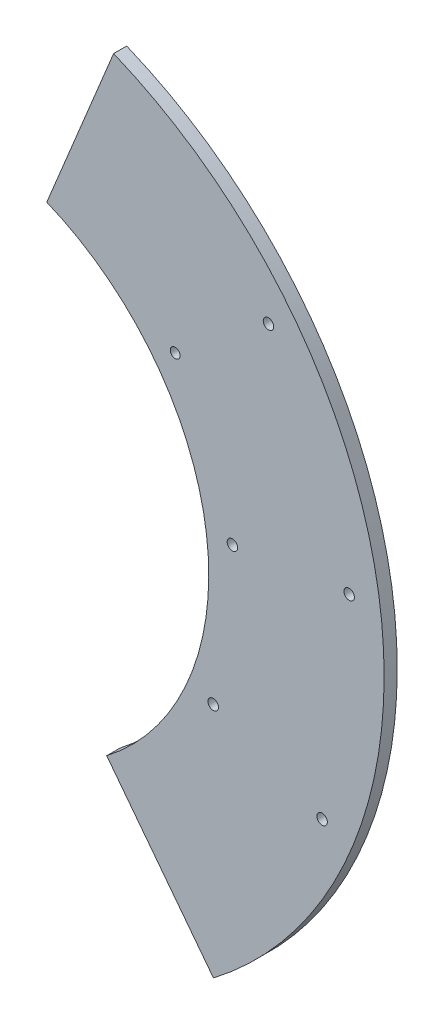
SolidWorks part; units mm, degrees
ref_plane "Plan de face" through (0, 0, 0) normal (0, 0, 1) x (1, 0, 0)
ref_plane "Plan de dessus" through (0, 0, 0) normal (0, 1, 0) x (1, 0, 0)
ref_plane "Plan de droite" through (0, 0, 0) normal (1, 0, 0) x (0, 0, -1)
sketch "Esquisse1" plane through (0, 0, 0) normal (0, 0, 1) x (1, 0, 0)
  line L2 (-2, 166.988) -> (-2, 99.98)
  line L3 (-2, -99.98) -> (-2, -166.988)
  arc A1 (0, -133.5) -> (0, 133.5) centre (0, 0) ccw
  arc A12 (-2, -166.988) -> (-2, 166.988) centre (0, 0) ccw
  arc A13 (-2, -99.98) -> (-2, 99.98) centre (0, 0) ccw
  point P0 (0, 0)
  point P1 (133.5, 0)
  point P4 (102, 0)
  point P5 (0, 0)
  point P7 (0, 165)
  point P8 (0, 102)
  point P9 (0, -102)
  point P10 (0, -165)
  point P11 (157.7903, 48.2413)
  point P42 (0, 0)
extrude "Boss.-Extru.2" add sketch "Esquisse1" along normal blind 5
sketch "Esquisse2" plane through (0, 0, 5) normal (0, 0, 1) x (1, 0, 0)
  line L0 (38.1129, 92.4522) -> (63.6486, 154.3951)
  line L1 (41.1619, 99.8484) -> (38.1129, 92.4522) construction
  line L2 (63.6486, 154.3951) -> (59.8373, 145.1499) construction
  line L3 (63.6486, 154.3951) -> (68.0288, 172.2752)
  line L4 (68.0288, 172.2752) -> (-24.9555, 192.9143)
  line L5 (-24.9555, 192.9143) -> (-14.9881, 82.8015)
  line L6 (-14.9881, 82.8015) -> (56.1922, 19.6454)
  line L7 (56.1922, 19.6454) -> (53.907, -84.2261)
  line L8 (53.907, -84.2261) -> (102.4159, -133.0072)
  line L9 (217.8754, -118.1368) -> (49.268, -139.8523) construction
  line L10 (95.7849, -124.3956) -> (101.8858, -132.3188) construction
  line L11 (102.4159, -133.0072) -> (102.4159, -156.0251)
  line L12 (102.4159, -156.0251) -> (-11.1483, -184.4376)
  line L13 (-11.1483, -184.4376) -> (38.1129, 92.4522)
  arc A0 (-2, -99.98) -> (-2, 99.98) centre (0, 0) ccw construction
  arc A1 (-2, -166.988) -> (-2, 166.988) centre (0, 0) ccw construction
  arc M1 (-2, 99.98) -> (-2, -99.98) centre (0, 0) cw
  line M2 (-2, -99.98) -> (-2, -166.988)
  arc M3 (-2, -166.988) -> (-2, 166.988) centre (0, 0) ccw
  line M4 (-2, 166.988) -> (-2, 99.98)
extrude "Enlèv. mat.-Extru.1" cut sketch "Esquisse2" against normal blind 10 contours L13 L11 L8 M2 M3 M1 | L0 M1 M3 M4
sketch "Esquisse3" plane through (0, 0, 5) normal (0, 0, 1) x (1, 0, 0)
  line L1 (25.4042, -95.1848) -> (-45.4208, -95.1848)
  line L2 (25.4042, -95.1848) -> (25.4042, -147.3571)
  line L3 (25.4042, -147.3571) -> (-45.4208, -147.3571)
  line L4 (-45.4208, -95.1848) -> (-45.4208, -147.3571)
extrude "Enlèv. mat.-Extru.2" cut sketch "Esquisse3" against normal blind 10
sketch "Esquisse4" plane through (0, 0, 5) normal (0, 0, 1) x (1, 0, 0)
  circle A0 centre (109.0346, 14.5413) radius 2
  circle A1 centre (101.6974, -41.9242) radius 2
  circle A2 centre (87.1561, 67.1104) radius 1.8701
  circle A3 centre (122.8109, 94.5647) radius 2
  circle A4 centre (143.3009, -59.075) radius 2
  circle A5 centre (153.6397, 20.49) radius 2
extrude "Enlèv. mat.-Extru.3" cut sketch "Esquisse4" against normal blind 10
sketch "Esquisse5" plane through (0, 0, 5) normal (0, 0, 1) x (1, 0, 0)
  line L0 (61.0095, -79.2328) -> (101.7983, -132.3862)
  line L1 (61.0095, -79.2328) -> (65.8902, -85.5715) construction
  line L2 (101.7983, -132.3862) -> (46.6435, -98.8972)
  line L3 (46.6435, -98.8972) -> (43.2157, -74.1968)
  line L4 (43.2157, -74.1968) -> (51.8402, -72.9999)
  line L5 (51.8402, -72.9999) -> (61.0095, -79.2328)
  arc A0 (53.907, -84.2261) -> (38.1129, 92.4522) centre (0, 0) ccw construction
extrude "Enlèv. mat.-Extru.4" cut sketch "Esquisse5" against normal blind 10
